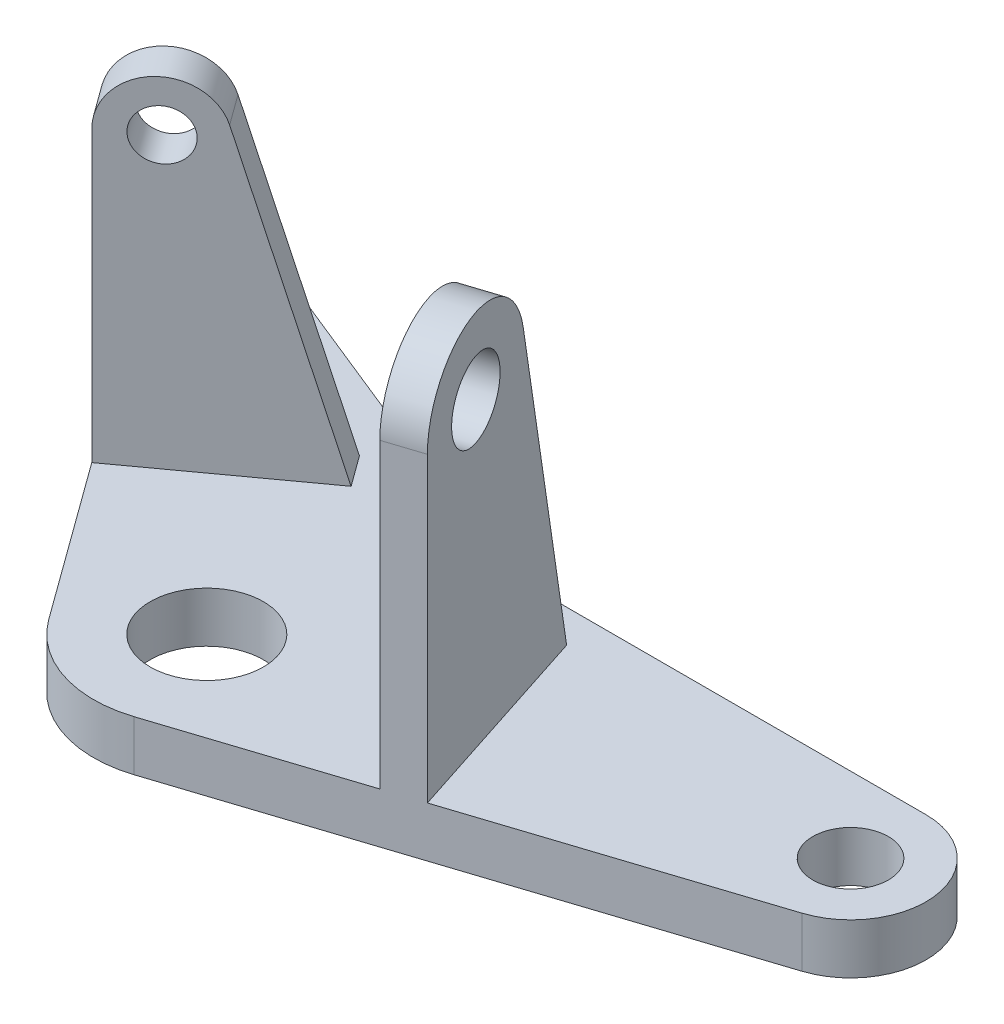
SolidWorks part; units mm, degrees
material "1060 Alloy"
ref_plane "Front Plane" through (0, 0, 0) normal (0, 0, 1) x (1, 0, 0)
ref_plane "Top Plane" through (0, 0, 0) normal (0, 1, 0) x (1, 0, 0)
ref_plane "Right Plane" through (0, 0, 0) normal (1, 0, 0) x (0, 0, -1)
sketch "Sketch1" plane through (0, 0, 0) normal (0, 1, 0) x (1, 0, 0)
  line L4 (82, 32.3346) -> (22.8999, 32.3346)
  line L5 (7.1664, 35.3929) -> (-45.0031, 56.4708)
  line L6 (-54.4721, 44.351) -> (-14.5623, -10.5801)
  line L7 (5.5623, -17.119) -> (85.7082, 8.922)
  circle A0 centre (0, 0) radius 9
  circle A1 centre (82, 20.3346) radius 6
  circle A2 centre (-48, 49.0533) radius 4
  arc A3 (85.7082, 8.922) -> (82, 32.3346) centre (82, 20.3346) ccw
  arc A4 (-45.0031, 56.4708) -> (-54.4721, 44.351) centre (-48, 49.0533) ccw
  arc A5 (-14.5623, -10.5801) -> (5.5623, -17.119) centre (0, 0) ccw
  arc A6 (22.8999, 32.3346) -> (7.1664, 35.3929) centre (22.8999, 74.3346) cw
  point P17 (-41.0884, 39.5403)
  point P18 (72.3942, 17.2135)
  point P21 (0, 0)
  point P23 (33.279, -17.1895)
  dimension "D1" = 8
  dimension "D2" = 12
  dimension "D3" = 18
  dimension "D4" = 24
  dimension "D5" = 16
  dimension "D6" = 36
  dimension "D10" = 42
  dimension "D7" = 22
  dimension "D8" = 18
  dimension "D9" = 54
  dimension "D11" = 48
  dimension "D12" = 82
extrude "Boss-Extrude1" add sketch "Sketch1" along normal blind 8
sketch "Sketch2" plane through (0, 8, 0) normal (0, 1, 0) x (1, 0, 0)
  line L0 (37.8982, -6.6124) -> (25.2436, 32.3346) construction
  line L1 (5.5623, -17.119) -> (85.7082, 8.922) construction
  line L2 (82, 32.3346) -> (22.8999, 32.3346) construction
  line L3 (-34.547, 16.9264) -> (-3.3063, 39.6242) construction
  line L4 (-54.4721, 44.351) -> (-14.5623, -10.5801) construction
  line L5 (7.1664, 35.3929) -> (-45.0031, 56.4708) construction
  dimension "D1" = 34
  dimension "D2" = 34
ref_plane "Plane1" through (-19.9847, 0, -27.5066) normal (0.5878, 0, 0.809) x (0.809, 0, -0.5878)
ref_plane "Plane2" through (32.3359, 0, -10.5066) normal (0.9511, 0, -0.309) x (-0.309, 0, -0.9511)
sketch "Sketch3" plane through (-19.9847, 0, -27.5066) normal (0.5878, 0, 0.809) x (0.809, 0, -0.5878)
  line L0 (-18, 8) -> (11.5127, 8)
  line L1 (11.5127, 8) -> (-2.3099, 56.2051)
  line L2 (-18, 8) -> (-18, 54)
  circle A0 centre (-10, 54) radius 4
  arc A1 (-2.3099, 56.2051) -> (-18, 54) centre (-10, 54) ccw
  point P6 (0, 0)
  point P9 (0, 0)
  point P10 (0, 0)
  point P11 (0, 0)
  dimension "D1" = 16
  dimension "D2" = 8
  dimension "D3" = 16
  dimension "D4" = 46
extrude "Boss-Extrude2" add sketch "Sketch3" along normal mid plane 6
sketch "Sketch4" plane through (32.3359, 0, -10.5066) normal (0.9511, 0, -0.309) x (-0.309, 0, -0.9511)
  line L0 (-18, 8) -> (-18, 56)
  line L1 (-18, 8) -> (16.4708, 8)
  line L2 (16.4708, 8) -> (5.7378, 58.4949)
  circle A0 centre (-6, 56) radius 6
  arc A1 (5.7378, 58.4949) -> (-18, 56) centre (-6, 56) ccw
  point P8 (0, 0)
  point P9 (0, 0)
  dimension "D2" = 12
  dimension "D3" = 24
  dimension "D1" = 12
  dimension "D4" = 48
extrude "Boss-Extrude3" add sketch "Sketch4" along normal mid plane 6
